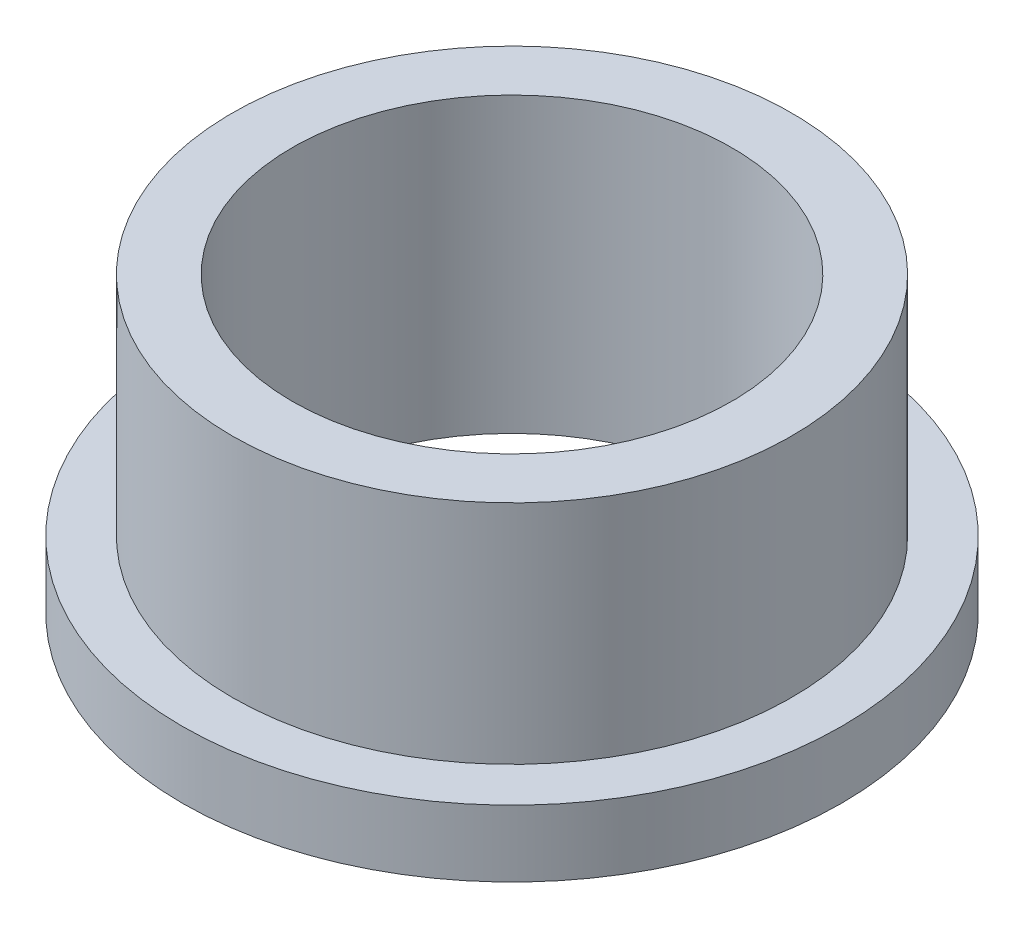
SolidWorks part; units mm, degrees
ref_plane "Front Plane" through (0, 0, 0) normal (0, 0, 1) x (1, 0, 0)
ref_plane "Top Plane" through (0, 0, 0) normal (0, 1, 0) x (1, 0, 0)
ref_plane "Right Plane" through (0, 0, 0) normal (1, 0, 0) x (0, 0, -1)
sketch "Sketch1" plane through (0, 0, 0) normal (0, 0, 1) x (1, 0, 0)
  line L0 (-4.95, 0) -> (-3.3, 0)
  line L1 (-4.95, 0) -> (-4.95, 1)
  line L2 (-4.95, 1) -> (-4.2, 1)
  line L3 (-4.2, 1) -> (-4.2, 4.4)
  line L4 (-4.2, 4.4) -> (-3.3, 4.4)
  line L5 (-3.3, 4.4) -> (-3.3, 0)
  dimension "D1" = 4.4
  dimension "D2" = 4.2
  dimension "D3" = 3.3
  dimension "D4" = 4.95
  dimension "D5" = 1
ref_axis "Axis1" through (0, 4.62, 0) along (0, -1, 0)
revolve "Revolve1" add sketch "Sketch1" angle 360 about axis through (0, 4.62, 0) along (0, -1, 0)
